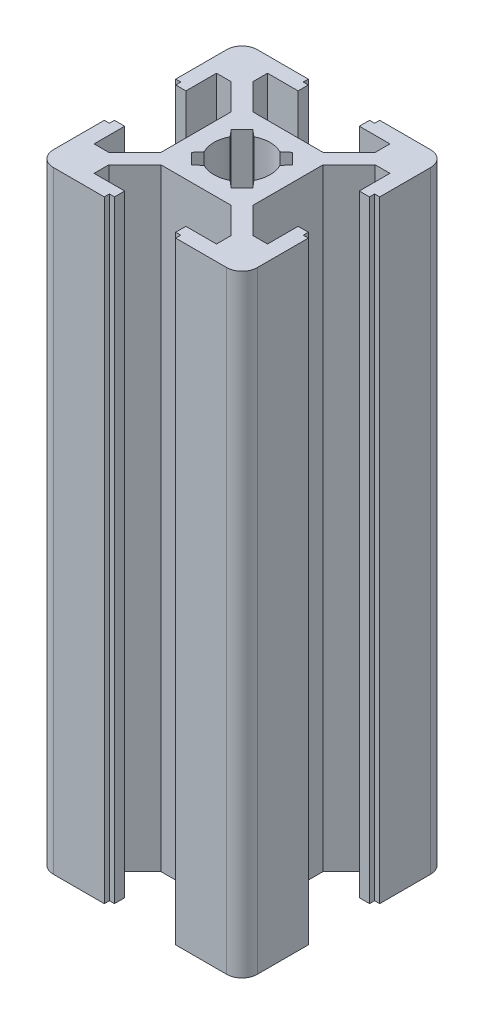
SolidWorks part; units mm, degrees
material "3.3547 (EN-AW 5083)"
ref_plane "Płaszczyzna przednia" through (0, 0, 0) normal (0, 0, 1) x (1, 0, 0)
ref_plane "Płaszczyzna górna" through (0, 0, 0) normal (0, 1, 0) x (1, 0, 0)
ref_plane "Płaszczyzna prawa" through (0, 0, 0) normal (1, 0, 0) x (0, 0, -1)
sketch "Szkic1" plane through (0, 0, 0) normal (0, 1, 0) x (1, 0, 0)
  line L0 (0, 10) -> (0, -10) construction
  line L1 (4.5, -4.5) -> (-4.5, -4.5)
  line L2 (4.5, -4.5) -> (4.5, 4.5)
  line L3 (4.5, 4.5) -> (-4.5, 4.5)
  line L4 (-4.5, -4.5) -> (-4.5, 4.5)
  line L5 (4.5, -4.5) -> (-4.5, 4.5) construction
  line L6 (4.5, 4.5) -> (-4.5, -4.5) construction
  line L7 (8.5, -10) -> (-8.5, -10)
  line L8 (10, -8.5) -> (10, 8.5)
  line L9 (8.5, 10) -> (-8.5, 10)
  line L10 (-10, -8.5) -> (-10, 8.5)
  line L11 (10, -10) -> (-10, 10) construction
  line L12 (10, 10) -> (-10, -10) construction
  line L13 (3.5, 10) -> (-3.5, 10)
  line L14 (-3.5, 10) -> (-3.5, 9.5)
  line L15 (-3.5, 9.5) -> (-3, 9.5)
  line L16 (-3, 9.5) -> (-3, 8.5)
  line L17 (-3, 8.5) -> (-6, 8.5)
  line L18 (-6, 8.5) -> (-6, 7.06)
  line L19 (-6, 7.06) -> (-3.4405, 4.5)
  line L20 (-1.9445, 3.0052) -> (-3.0052, 1.9445)
  line L21 (-1.9445, 3.0052) -> (-1.2713, 2.4385)
  line L22 (-3.0052, 1.9445) -> (-2.4385, 1.2713)
  line L23 (3.5, 10) -> (3.5, 9.5)
  line L24 (3.5, 9.5) -> (3, 9.5)
  line L25 (3, 9.5) -> (3, 8.5)
  line L26 (3, 8.5) -> (6, 8.5)
  line L27 (6, 8.5) -> (6, 7.06)
  line L28 (6, 7.06) -> (3.4405, 4.5)
  line L29 (1.9445, 3.0052) -> (3.0052, 1.9445)
  line L30 (1.9445, 3.0052) -> (1.2713, 2.4385)
  line L31 (3.0052, 1.9445) -> (2.4385, 1.2713)
  line L32 (1.9445, 3.0052) -> (1.2713, 2.4385)
  line L33 (3.0052, 1.9445) -> (1.9445, 3.0052)
  line L34 (3.0052, 1.9445) -> (2.4385, 1.2713)
  line L35 (7.06, 6) -> (4.5, 3.4405)
  line L36 (8.5, 6) -> (7.06, 6)
  line L37 (8.5, 3) -> (8.5, 6)
  line L38 (9.5, 3) -> (8.5, 3)
  line L39 (9.5, 3.5) -> (9.5, 3)
  line L40 (10, 3.5) -> (9.5, 3.5)
  line L41 (10, -3.5) -> (9.5, -3.5)
  line L42 (9.5, -3.5) -> (9.5, -3)
  line L43 (9.5, -3) -> (8.5, -3)
  line L44 (8.5, -3) -> (8.5, -6)
  line L45 (8.5, -6) -> (7.06, -6)
  line L46 (7.06, -6) -> (4.5, -3.4405)
  line L47 (3.0052, -1.9445) -> (2.4385, -1.2713)
  line L48 (3.0052, -1.9445) -> (1.9445, -3.0052)
  line L49 (1.9445, -3.0052) -> (1.2713, -2.4385)
  line L50 (3.0052, -1.9445) -> (2.4385, -1.2713)
  line L51 (1.9445, -3.0052) -> (3.0052, -1.9445)
  line L52 (1.9445, -3.0052) -> (1.2713, -2.4385)
  line L53 (6, -7.06) -> (3.4405, -4.5)
  line L54 (6, -8.5) -> (6, -7.06)
  line L55 (3, -8.5) -> (6, -8.5)
  line L56 (3, -9.5) -> (3, -8.5)
  line L57 (3.5, -9.5) -> (3, -9.5)
  line L58 (3.5, -10) -> (3.5, -9.5)
  line L59 (-3.5, -10) -> (-3.5, -9.5)
  line L60 (-3.5, -9.5) -> (-3, -9.5)
  line L61 (-3, -9.5) -> (-3, -8.5)
  line L62 (-3, -8.5) -> (-6, -8.5)
  line L63 (-6, -8.5) -> (-6, -7.06)
  line L64 (-6, -7.06) -> (-3.4405, -4.5)
  line L65 (-1.9445, -3.0052) -> (-1.2713, -2.4385)
  line L66 (-1.9445, -3.0052) -> (-3.0052, -1.9445)
  line L67 (-3.0052, -1.9445) -> (-2.4385, -1.2713)
  line L68 (-1.9445, -3.0052) -> (-1.2713, -2.4385)
  line L69 (-3.0052, -1.9445) -> (-1.9445, -3.0052)
  line L70 (-3.0052, -1.9445) -> (-2.4385, -1.2713)
  line L71 (-7.06, -6) -> (-4.5, -3.4405)
  line L72 (-8.5, -6) -> (-7.06, -6)
  line L73 (-8.5, -3) -> (-8.5, -6)
  line L74 (-9.5, -3) -> (-8.5, -3)
  line L75 (-9.5, -3.5) -> (-9.5, -3)
  line L76 (-10, -3.5) -> (-9.5, -3.5)
  line L77 (-10, 3.5) -> (-9.5, 3.5)
  line L78 (-9.5, 3.5) -> (-9.5, 3)
  line L79 (-9.5, 3) -> (-8.5, 3)
  line L80 (-8.5, 3) -> (-8.5, 6)
  line L81 (-8.5, 6) -> (-7.06, 6)
  line L82 (-7.06, 6) -> (-4.5, 3.4405)
  line L83 (-3.0052, 1.9445) -> (-2.4385, 1.2713)
  line L84 (-3.0052, 1.9445) -> (-1.9445, 3.0052)
  line L85 (-1.9445, 3.0052) -> (-1.2713, 2.4385)
  circle A0 centre (0, 0) radius 2.75
  arc A1 (10, -8.5) -> (8.5, -10) centre (8.5, -8.5) cw
  arc A2 (-10, -8.5) -> (-8.5, -10) centre (-8.5, -8.5) ccw
  arc A3 (10, 8.5) -> (8.5, 10) centre (8.5, 8.5) ccw
  arc A4 (-8.5, 10) -> (-10, 8.5) centre (-8.5, 8.5) ccw
  point P16 (0, 10)
  point P37 (-2.4749, 2.4749)
  dimension "D1" = 5.5
  dimension "D12" = 1.5
  dimension "D2" = 9
  dimension "D3" = 20
  dimension "D4" = 20
  dimension "D5" = 7
  dimension "D6" = 0.5
  dimension "D7" = 0.5
  dimension "D8" = 1
  dimension "D9" = 3
  dimension "D10" = 1.44
  dimension "D11" = 3.62
  dimension "D13" = 1.5
  dimension "D14" = 3.5
  dimension "D15" = 0.88
  dimension "D16" = 4
extrude "Dodanie-wyciągnięcie1" add sketch "Szkic1" along normal blind 60 contours L9 A4 L10 L77 L78 L79 L80 L81 L82 L4 L3 L19 L18 L17 L16 L15 L14 | L8 A3 L9 L23 L24 L25 L26 L27 L28 L3 L2 L35 L36 L37 L38 L39 L40 | L4 L1 L2 L3 A0 L47 L48 L49 L65 L66 L67 L22 L20 L21 L30 L29 L31 | L10 A2 L7 L59 L60 L61 L62 L63 L64 L1 L4 L71 L72 L73 L74 L75 L76 | A1 L8 L41 L42 L43 L44 L45 L46 L2 L1 L53 L54 L55 L56 L57 L58 L7
